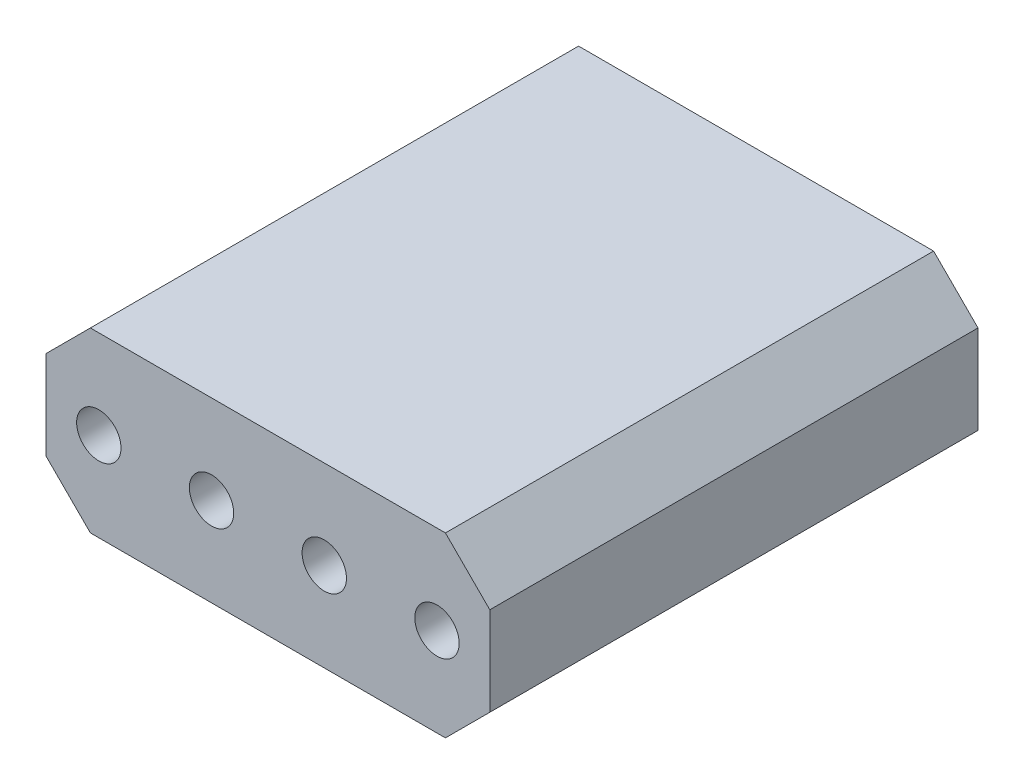
SolidWorks part; units mm, degrees
ref_plane "Спереди" through (0, 0, 0) normal (0, 0, 1) x (1, 0, 0)
ref_plane "Сверху" through (0, 0, 0) normal (0, 1, 0) x (1, 0, 0)
ref_plane "Справа" through (0, 0, 0) normal (1, 0, 0) x (0, 0, -1)
sketch "Эскиз5" plane through (0, 0, 0) normal (0, 0, 1) x (1, 0, 0)
  line L0 (-3.46, 0.35) -> (-3.46, -0.35)
  line L2 (-4.16, -0.35) -> (-4.16, 0.35)
  line L4 (4.16, -0.35) -> (4.16, 0.35)
  line L5 (-4.16, -0.35) -> (4.16, 0.35) construction
  line L6 (-4.16, 0.35) -> (4.16, -0.35) construction
  line L7 (-1.62, 0.35) -> (-1.62, -0.35)
  line L8 (-0.92, 0.35) -> (-0.92, -0.35)
  line L9 (0.92, 0.35) -> (0.92, -0.35)
  line L10 (1.62, 0.35) -> (1.62, -0.35)
  line L11 (3.46, 0.35) -> (3.46, -0.35)
  line L12 (-4.16, -0.35) -> (-3.46, -0.35)
  line L13 (-5, -2) -> (5, -2)
  line L14 (-5, -2) -> (-5, 2)
  line L15 (-5, 2) -> (5, 2)
  line L16 (5, -2) -> (5, 2)
  line L17 (-5, -2) -> (5, 2) construction
  line L18 (-5, 2) -> (5, -2) construction
  line L19 (-4.16, 0.35) -> (-3.46, 0.35)
  line L20 (-1.62, 0.35) -> (-0.92, 0.35)
  line L21 (-1.62, -0.35) -> (-0.92, -0.35)
  line L22 (0.92, 0.35) -> (1.62, 0.35)
  line L23 (0.92, -0.35) -> (1.62, -0.35)
  line L24 (3.46, 0.35) -> (4.16, 0.35)
  line L25 (4.16, -0.35) -> (3.46, -0.35)
  point P0 (0, 0)
  point P18 (0, 0)
  point P22 (-1.62, 0)
  dimension "D1" = 0.7
  dimension "D2" = 8.32
  dimension "D3" = 0.7
  dimension "D4" = 1.84
  dimension "D5" = 0.7
  dimension "D6" = 1.84
  dimension "D7" = 0.7
  dimension "D8" = 1.84
  dimension "D9" = 10
  dimension "D10" = 4
extrude "Бобышка-Вытянуть2" add sketch "Эскиз5" along normal blind 8
sketch "Эскиз6" plane through (0, 0, 8) normal (0, 0, 1) x (1, 0, 0)
  line L0 (-4.16, 0) -> (-3.46, 0) construction
  line L1 (-5, -2) -> (5, -2)
  line L2 (-5, -2) -> (-5, 2)
  line L3 (-5, 2) -> (5, 2)
  line L4 (5, -2) -> (5, 2)
  line L5 (-5, -2) -> (5, 2) construction
  line L6 (-5, 2) -> (5, -2) construction
  line L7 (-4.16, 0.35) -> (-4.16, -0.35) construction
  line L8 (-3.46, -0.35) -> (-3.46, 0.35) construction
  line L9 (-1.62, 0) -> (-0.92, 0) construction
  line L10 (-1.62, 0.35) -> (-1.62, -0.35) construction
  line L11 (-0.92, -0.35) -> (-0.92, 0.35) construction
  line L12 (0.92, 0) -> (1.62, 0) construction
  line L13 (0.92, 0.35) -> (0.92, -0.35) construction
  line L14 (1.62, -0.35) -> (1.62, 0.35) construction
  line L15 (3.46, 0) -> (4.16, 0) construction
  line L16 (3.46, 0.35) -> (3.46, -0.35) construction
  line L17 (4.16, -0.35) -> (4.16, 0.35) construction
  circle A0 centre (-3.81, 0) radius 0.5
  circle A1 centre (-1.27, 0) radius 0.5
  circle A2 centre (1.27, 0) radius 0.5
  circle A3 centre (3.81, 0) radius 0.5
  point P0 (0, 0)
extrude "Бобышка-Вытянуть3" add sketch "Эскиз6" along normal blind 3
chamfer "Фаска3" distance 1 angle 45 4 edges at (5, 2, 5.5) (5, -2, 5.5) (-5, -2, 5.5) (-5, 2, 5.5)
